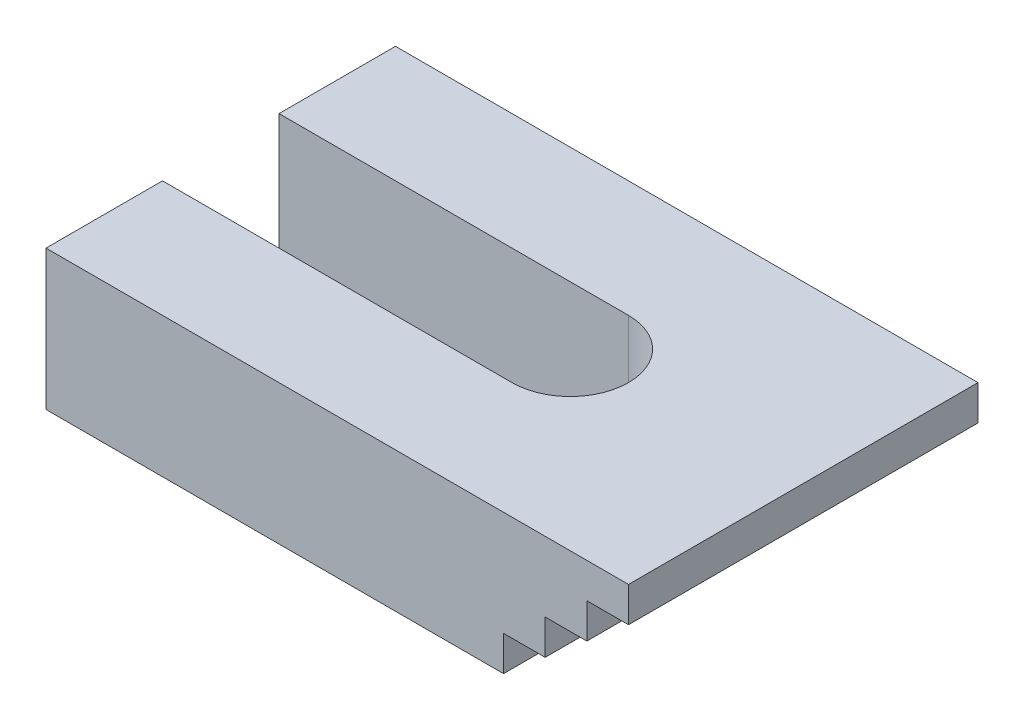
SolidWorks part; units mm, degrees
ref_plane "Plan de face" through (0, 0, 0) normal (0, 0, 1) x (1, 0, 0)
ref_plane "Plan de dessus" through (0, 0, 0) normal (0, 1, 0) x (1, 0, 0)
ref_plane "Plan de droite" through (0, 0, 0) normal (1, 0, 0) x (0, 0, -1)
sketch "Esquisse1" plane through (0, 0, 0) normal (0, 0, 1) x (1, 0, 0)
  line L0 (27.1505, 6) -> (7.1505, 6)
  line L1 (0, 0) -> (20, 0)
  line L2 (0, 0) -> (0, 3)
  line L5 (23.5753, 3) -> (3.5753, 3)
  line L6 (34.301, 12) -> (20, 0)
  line L7 (3.5753, 3) -> (0, 3)
  line L8 (7.1505, 6) -> (7.1505, 9)
  line L9 (3.5753, 3) -> (3.5753, 6)
  line L10 (3.5753, 6) -> (7.1505, 6)
  line L11 (10.7258, 9) -> (10.7258, 12)
  line L12 (10.7258, 12) -> (34.301, 12)
  line L13 (7.1505, 9) -> (30.7258, 9)
  point P1 (0, 0)
  point P8 (0, 0)
  dimension "D1" = 40
  dimension "D2" = 3
  dimension "D3" = 3
  dimension "D4" = 3
  dimension "D5" = 20
  dimension "D6" = 20
  dimension "D7" = 20
  dimension "D8" = 3
  dimension "D9" = 20
sketch "Esquisse2" plane through (0, 0, 0) normal (0, 0, 1) x (1, 0, 0)
  line L0 (0, 0) -> (-39.2742, 0)
  line L1 (-39.2742, 0) -> (-39.2742, 12)
  line L2 (10.7258, 12) -> (-39.2742, 12)
  line L3 (0, 0) -> (0, 3)
  line L4 (0, 3) -> (3.5753, 3)
  line L5 (3.5753, 3) -> (3.5753, 6)
  line L6 (3.5753, 6) -> (7.1505, 6)
  line L7 (7.1505, 6) -> (7.1505, 9)
  line L8 (7.1505, 9) -> (10.7258, 9)
  line L9 (10.7258, 9) -> (10.7258, 12)
  dimension "D1" = 3.5753
  dimension "D2" = 3
  dimension "D3" = 3
  dimension "D4" = 3
  dimension "D5" = 3
  dimension "D6" = 3.5753
  dimension "D7" = 3.5753
  dimension "D8" = 3.5753
  dimension "D9" = 50
extrude "Boss.-Extru.1" add sketch "Esquisse2" along normal blind 30
sketch "Esquisse3" plane through (0, 0, 0) normal (0, -1, 0) x (1, 0, 0)
  line L0 (-39.2742, 15) -> (-7.2847, 15) construction
  line L1 (-39.2742, 30) -> (-39.2742, 0) construction
  line L2 (-9.2742, 10) -> (-39.2742, 10)
  line L3 (-9.2742, 20) -> (-39.2742, 20)
  line L4 (-39.2742, 20) -> (-39.2742, 10)
  arc A0 (-9.2742, 10) -> (-9.2742, 20) centre (-9.2742, 15) ccw
  dimension "D1" = 10
  dimension "D2" = 30
extrude "Enlèv. mat.-Extru.1" cut sketch "Esquisse3" against normal through all
